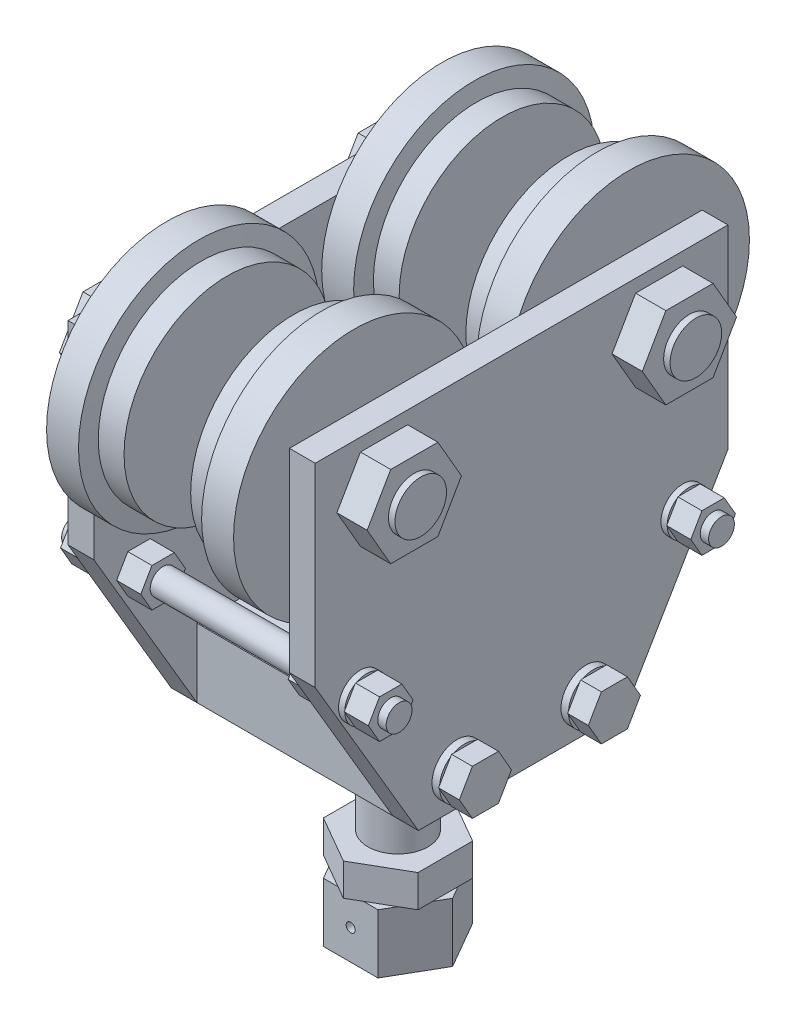
SolidWorks part; units mm, degrees
ref_plane "Front" through (0, 0, 0) normal (0, 0, 1) x (1, 0, 0)
ref_plane "Top" through (0, 0, 0) normal (0, 1, 0) x (1, 0, 0)
ref_plane "Right" through (0, 0, 0) normal (1, 0, 0) x (0, 0, -1)
ref_plane "Z PLANE" through (0, 0, 0) normal (0, 0, 1) x (1, 0, 0)
ref_plane "YOKE BOTTOM" through (0, 0, 0) normal (0, 1, 0) x (-1, 0, 0)
ref_plane "X PLANE" through (0, 0, 0) normal (1, 0, 0) x (0, 0, -1)
sketch "YOKE CROSS SECTION" plane through (0, 0, 0) normal (1, 0, 0) x (0, 0, -1)
  line L0 (0, 0) -> (0, 57.0916) construction
  line L1 (0, 84.8167) -> (0, -84.8167) construction
  line L2 (-76.2, 0) -> (76.2, 0)
  line L3 (69.1602, 0) -> (-69.1602, 0) construction
  line L4 (76.2, 0) -> (76.2, 50.8)
  line L5 (-76.2, 0) -> (-76.2, 50.8)
  line L6 (76.2, 50.8) -> (-76.2, 50.8)
  point P12 (0, 50.8)
  dimension "D1" = 50.8
  dimension "D2" = 152.4
ref_plane "1/2 YOKE LENGTH (A)" through (72.2313, 0, 0) normal (1, 0, 0) x (0, 0, -1)
ref_plane "WHEEL LOCATION" through (0, 0, 101.6) normal (0, 0, 1) x (1, 0, 0)
extrude "YOKE" add sketch "YOKE CROSS SECTION" along normal up to surface (72.2313 mm away) up to plane "1/2 YOKE LENGTH (A)"
sketch "SIDEPLATE PROFILE" plane through (72.2313, 0, 0) normal (1, 0, 0) x (0, 0, -1)
  line L0 (-152.4, 273.05) -> (152.4, 273.05)
  line L1 (0, 84.8167) -> (0, -84.8167) construction
  line L2 (152.4, 129.54) -> (76.2, 0)
  line L3 (-152.4, 129.54) -> (-76.2, 0)
  line L4 (0, 0) -> (-76.2, 0)
  line L5 (0, 0) -> (76.2, 0)
  line L6 (-152.4, 273.05) -> (-152.4, 129.54)
  line L7 (152.4, 129.54) -> (152.4, 273.05)
  line L8 (69.1602, 0) -> (-69.1602, 0) construction
  dimension "D1" = 76.2
  dimension "D2" = 76.2
  dimension "D3" = 76.2
  dimension "D4" = 76.2
  dimension "D5" = 129.54
  dimension "D6" = 143.51
  dimension "D7" = 129.54
ref_plane "WHEEL HEIGHT" through (0, 233.3625, 0) normal (0, 1, 0) x (-1, 0, 0)
ref_plane "YOKE SCREW LOCATION Z" through (0, 0, 47.625) normal (0, 0, 1) x (1, 0, 0)
ref_plane "YOKE SCREW LOCATION Y" through (0, 25.4, 0) normal (0, 1, 0) x (-1, 0, 0)
extrude "SIDEPLATE" add sketch "SIDEPLATE PROFILE" along normal blind 19.05
sketch "WHEEL PIN NUT PROFILE" plane through (91.2812, 0, 0) normal (1, 0, 0) x (0, 0, -1)
  line L0 (-101.6, 89.3799) -> (-101.6, -89.3799) construction
  line L1 (-66.7713, 233.3625) -> (-84.1857, 263.525)
  line L2 (-84.1857, 263.525) -> (-119.0143, 263.525)
  line L3 (-119.0143, 263.525) -> (-136.4287, 233.3625)
  line L4 (-136.4287, 233.3625) -> (-119.0143, 203.2)
  line L5 (-119.0143, 203.2) -> (-84.1857, 203.2)
  line L6 (-84.1857, 203.2) -> (-66.7713, 233.3625)
  line L7 (69.1602, 233.3625) -> (-69.1602, 233.3625) construction
  circle A0 centre (-101.6, 233.3625) radius 13.4938 construction
  dimension "D1" = 60.325
extrude "WHEEL PIN NUT" add sketch "WHEEL PIN NUT PROFILE" along normal blind 22.352
sketch "WHEEL PIN PROJECTION PROFILE" plane through (113.6332, 0, 0) normal (1, 0, 0) x (0, 0, -1)
  line L0 (-101.6, 89.3799) -> (-101.6, -89.3799) construction
  line L3 (69.1602, 233.3625) -> (-69.1602, 233.3625) construction
  circle A0 centre (-101.6, 233.3625) radius 19.05
  dimension "D1" = 38.1
extrude "WHEEL PIN PROJECTION" add sketch "WHEEL PIN PROJECTION PROFILE" along normal blind 4.7625
sketch "LOCKNUTS PROFILE" plane through (91.2812, 0, 0) normal (1, 0, 0) x (0, 0, -1)
  line L0 (-47.625, 84.8167) -> (-47.625, -84.8167) construction
  line L1 (50, 25.4) -> (-50, 25.4) construction
  circle A0 centre (-47.625, 25.4) radius 18.542
  dimension "D1" = 37.084
extrude "LOCKNUTS" add sketch "LOCKNUTS PROFILE" along normal blind 5.5626
sketch "SCREWS PROFILE" plane through (96.8438, 0, 0) normal (1, 0, 0) x (0, 0, -1)
  line L0 (50, 25.4) -> (-50, 25.4) construction
  line L1 (-28.3776, 25.4) -> (-38.0013, 42.0688)
  line L2 (-38.0013, 42.0688) -> (-57.2487, 42.0688)
  line L3 (-57.2487, 42.0688) -> (-66.8724, 25.4)
  line L4 (-66.8724, 25.4) -> (-57.2487, 8.7313)
  line L5 (-57.2487, 8.7313) -> (-38.0013, 8.7313)
  line L6 (-38.0013, 8.7313) -> (-28.3776, 25.4)
  line L7 (-47.625, 84.8167) -> (-47.625, -84.8167) construction
  circle A0 centre (-47.625, 25.4) radius 16.6687 construction
  dimension "D1" = 33.3375
extrude "SCREWS" add sketch "SCREWS PROFILE" along normal blind 15.3416
sketch "PROFILE" plane through (0, 50.8, 0) normal (0, 1, 0) x (-1, 0, 0)
  line L0 (84.8167, 0) -> (-84.8167, 0) construction
  line L1 (0, 83.2389) -> (0, -83.2389) construction
  circle A0 centre (0, 0) radius 30.1625
  dimension "D1" = 60.325
extrude "KING BOLT HEAD" add sketch "PROFILE" along normal blind 38.1
mirror "Mirror1" about plane through (0, 0, 0) normal (0, 0, 1) of "WHEEL PIN PROJECTION", "WHEEL PIN NUT"
mirror "Mirror YOKE SCREWS" about plane through (0, 0, 0) normal (0, 0, 1) of "SCREWS", "LOCKNUTS"
mirror "Mirror SIDE 1" about plane through (0, 0, 0) normal (1, 0, 0) of bodies 112
ref_plane "TOP OF NUT" through (0, -83.0521, 0) normal (0, 1, 0) x (-1, 0, 0)
sketch "DIA." plane through (0, 0, 0) normal (0, -1, 0) x (1, 0, 0)
  line L0 (84.8167, 0) -> (-84.8167, 0) construction
  line L1 (0, -83.2389) -> (0, 83.2389) construction
  circle A0 centre (0, 0) radius 22.225
  dimension "D1" = 44.45
extrude "KING BOLT" add sketch "DIA." along normal up to surface (83.0521 mm away) up to plane "TOP OF NUT"
sketch "KING BOLT JAN NUT PROFILE" plane through (0, -83.0521, 0) normal (0, -1, 0) x (1, 0, 0)
  line L0 (84.8167, 0) -> (-84.8167, 0) construction
  line L1 (0, -40.3279) -> (34.925, -20.164)
  line L2 (34.925, -20.164) -> (34.925, 20.164)
  line L3 (34.925, 20.164) -> (0, 40.3279)
  line L4 (0, 40.3279) -> (-34.925, 20.164)
  line L5 (-34.925, 20.164) -> (-34.925, -20.164)
  line L6 (-34.925, -20.164) -> (0, -40.3279)
  line L7 (0, -83.2389) -> (0, 83.2389) construction
  circle A0 centre (0, 0) radius 34.925 construction
  dimension "D1" = 69.85
extrude "KING BOLT JAM NUT" add sketch "KING BOLT JAN NUT PROFILE" along normal blind 23.8125
sketch "KING BOLT NUT PROFILE" plane through (0, -106.8646, 0) normal (0, -1, 0) x (1, 0, 0)
  line L1 (40.3279, 0) -> (20.164, 34.925)
  line L2 (20.164, 34.925) -> (-20.164, 34.925)
  line L3 (-20.164, 34.925) -> (-40.3279, 0)
  line L4 (-40.3279, 0) -> (-20.164, -34.925)
  line L5 (-20.164, -34.925) -> (20.164, -34.925)
  line L6 (20.164, -34.925) -> (40.3279, 0)
  line L10 (0, -83.2389) -> (0, 83.2389) construction
  line L11 (84.8167, 0) -> (-84.8167, 0) construction
  circle A0 centre (0, 0) radius 34.925 construction
  dimension "D1" = 69.85
extrude "KING BOLT NUT" add sketch "KING BOLT NUT PROFILE" along normal blind 43.6372
sketch "Sketch5" plane through (0, -150.5018, 0) normal (0, -1, 0) x (1, 0, 0)
  circle A0 centre (0, 0) radius 22.225 construction
  circle A1 centre (0, 0) radius 22.225
extrude "EXTENDED KING BOLT" add sketch "Sketch5" along normal blind 9.525
chamfer "Chamfer1" distance 2.3812 angle 45 1 edges at (0, -160.0268, -22.225)
ref_plane "MOUNTING REF PLANE" through (0, -34.925, 0) normal (0, 1, 0) x (-1, 0, 0)
ref_plane "THREADED ROD LOCATION" through (0, 0, 119.0625) normal (0, 0, 1) x (1, 0, 0)
ref_plane "THREADED ROD HEIGHT" through (0, 107.95, 0) normal (0, 1, 0) x (-1, 0, 0)
sketch "Sketch6" plane through (72.2313, 0, 0) normal (1, 0, 0) x (0, 0, -1)
  line L0 (69.1602, 107.95) -> (-69.1602, 107.95) construction
  line L1 (-119.0625, 84.8167) -> (-119.0625, -84.8167) construction
  circle A0 centre (-119.0625, 107.95) radius 9.525
  dimension "D1" = 19.05
extrude "THREADED ROD" add sketch "Sketch6" along normal blind 47.625 and the other way up to surface (72.2313 mm away) other way up to plane "X PLANE"
sketch "Sketch7" plane through (72.2313, 0, 0) normal (1, 0, 0) x (0, 0, -1)
  line L0 (69.1602, 107.95) -> (-69.1602, 107.95) construction
  line L1 (-102.5647, 107.95) -> (-110.8136, 122.2375)
  line L2 (-110.8136, 122.2375) -> (-127.3114, 122.2375)
  line L3 (-127.3114, 122.2375) -> (-135.5603, 107.95)
  line L4 (-135.5603, 107.95) -> (-127.3114, 93.6625)
  line L5 (-127.3114, 93.6625) -> (-110.8136, 93.6625)
  line L6 (-110.8136, 93.6625) -> (-102.5647, 107.95)
  line L7 (-119.0625, 84.8167) -> (-119.0625, -84.8167) construction
  circle A0 centre (-119.0625, 107.95) radius 14.2875 construction
  dimension "D1" = 28.575
extrude "THREADED ROD NUTS INNER " add sketch "Sketch7" against normal blind 17.8054
sketch "Sketch8" plane through (91.2812, 0, 0) normal (1, 0, 0) x (0, 0, -1)
  line L0 (69.1602, 107.95) -> (-69.1602, 107.95) construction
  line L1 (-119.0625, 84.8167) -> (-119.0625, -84.8167) construction
  circle A0 centre (-119.0625, 107.95) radius 16.129
  dimension "D1" = 32.258
extrude "THREADED ROD LOCKWASHER " add sketch "Sketch8" along normal blind 4.572
sketch "Sketch9" plane through (95.8533, 0, 0) normal (1, 0, 0) x (0, 0, -1)
  line L0 (-102.5647, 107.95) -> (-110.8136, 122.2375) construction
  line L1 (-110.8136, 93.6625) -> (-102.5647, 107.95) construction
  line L2 (-127.3114, 93.6625) -> (-110.8136, 93.6625) construction
  line L3 (-135.5603, 107.95) -> (-127.3114, 93.6625) construction
  line L4 (-127.3114, 122.2375) -> (-135.5603, 107.95) construction
  line L5 (-110.8136, 122.2375) -> (-127.3114, 122.2375) construction
  line L6 (-102.5647, 107.95) -> (-110.8136, 122.2375)
  line L7 (-110.8136, 93.6625) -> (-102.5647, 107.95)
  line L8 (-127.3114, 93.6625) -> (-110.8136, 93.6625)
  line L9 (-135.5603, 107.95) -> (-127.3114, 93.6625)
  line L10 (-127.3114, 122.2375) -> (-135.5603, 107.95)
  line L11 (-110.8136, 122.2375) -> (-127.3114, 122.2375)
extrude "THREADED ROD NUT OUTER" add sketch "Sketch9" along normal blind 17.8054
mirror "Mirror2" about plane through (0, 0, 0) normal (0, 0, 1) of "THREADED ROD NUT OUTER", "THREADED ROD LOCKWASHER ", "THREADED ROD NUTS INNER ", "THREADED ROD"
mirror "Mirror3" about plane through (0, 0, 0) normal (1, 0, 0) of "Mirror2", "THREADED ROD", "THREADED ROD NUTS INNER ", "THREADED ROD LOCKWASHER ", "THREADED ROD NUT OUTER"
sketch "Sketch10" plane through (0, 0, 34.925) normal (0, 0, 1) x (1, 0, 0)
  line L0 (0, -83.2389) -> (0, 83.2389) construction
  line L1 (-20.164, -150.5018) -> (-40.3279, -150.5018) construction
  circle A0 centre (0, -128.2768) radius 3.3655
  dimension "D1" = 6.731
  dimension "D2" = 22.225
extrude "COTTER PIN HOLE" cut sketch "Sketch10" against normal through all
sketch "Sketch11" plane through (0, 0, 101.6) normal (0, 0, 1) x (1, 0, 0)
  line L0 (72.2313, 260.35) -> (72.2313, 233.3625)
  line L1 (24.6063, 309.4907) -> (24.6063, 233.3625)
  line L2 (72.2313, 233.3625) -> (24.6063, 233.3625)
  line L3 (69.0563, 322.2625) -> (69.0563, 260.35)
  line L4 (72.2313, 260.35) -> (69.0563, 260.35)
  line L5 (69.0563, 322.2625) -> (45.4512, 322.2625)
  line L6 (43.6563, 309.4907) -> (24.6063, 309.4907)
  line L7 (69.1602, 233.3625) -> (-69.1602, 233.3625) construction
  line L8 (72.2313, -75.0522) -> (72.2313, 75.0522) construction
  line L9 (43.6563, 309.4907) -> (45.4512, 322.2625)
  dimension "D5" = 26.9875
  dimension "D1" = 47.625
  dimension "D2" = 3.175
  dimension "D3" = 26.78
  dimension "D4" = 28.575
  dimension "D6" = 88.9
  dimension "D7" = 76.1282
revolve "WHEEL" add sketch "Sketch11" angle 360 about axis through (118.3957, 233.3625, 101.6) along (-1, 0, 0)
mirror "Mirror4" about plane through (0, 0, 0) normal (0, 0, 1) of "WHEEL"
mirror "Mirror5" about plane through (0, 0, 0) normal (1, 0, 0) of "Mirror4", "WHEEL"
sketch "Sketch12" plane through (0, 0, 0) normal (0, -1, 0) x (1, 0, 0)
  circle A0 centre (0, 0) radius 25.4
  circle A1 centre (0, 0) radius 30.1625
  dimension "D1" = 50.8
  dimension "D2" = 60.325
extrude "SPACER" add sketch "Sketch12" along normal blind 12.7
ref_plane "TREAD OF TRACK" through (0, 157.1625, 0) normal (0, 1, 0) x (-1, 0, 0)
